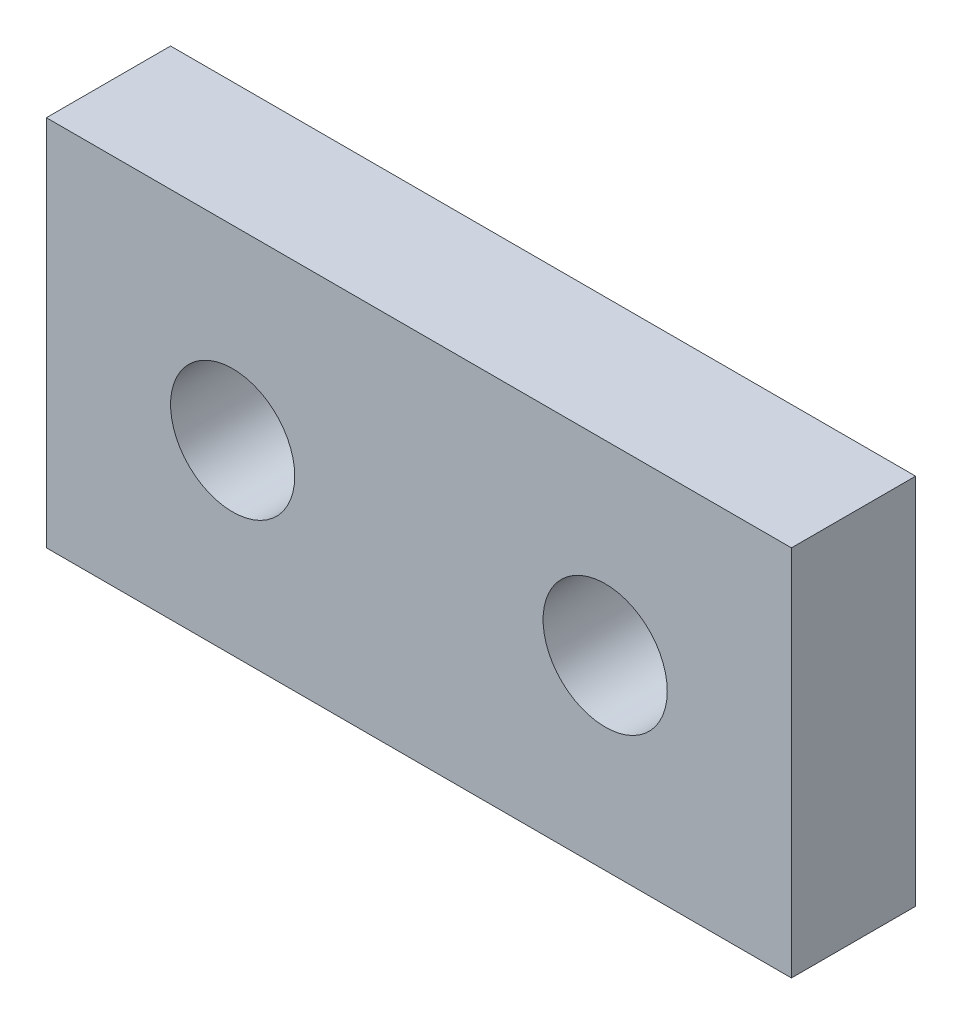
SolidWorks part; units mm, degrees
ref_plane "Front Plane" through (0, 0, 0) normal (0, 0, 1) x (1, 0, 0)
ref_plane "Top Plane" through (0, 0, 0) normal (0, 1, 0) x (1, 0, 0)
ref_plane "Right Plane" through (0, 0, 0) normal (1, 0, 0) x (0, 0, -1)
sketch "Sketch1" plane through (0, 0, 0) normal (0, 0, 1) x (1, 0, 0)
  line L0 (0, 0) -> (60, 0)
  line L1 (60, 0) -> (60, 30)
  line L2 (60, 30) -> (0, 30)
  line L3 (0, 30) -> (0, 0)
  circle A0 centre (15, 15) radius 5
  circle A1 centre (45, 15) radius 5
  dimension "D3" = 10
  dimension "D7" = 30
  dimension "D1" = 30
  dimension "D2" = 60
  dimension "D4" = 15
  dimension "D5" = 15
  dimension "D6" = 2
extrude "Boss-Extrude1" add sketch "Sketch1" along normal blind 10
